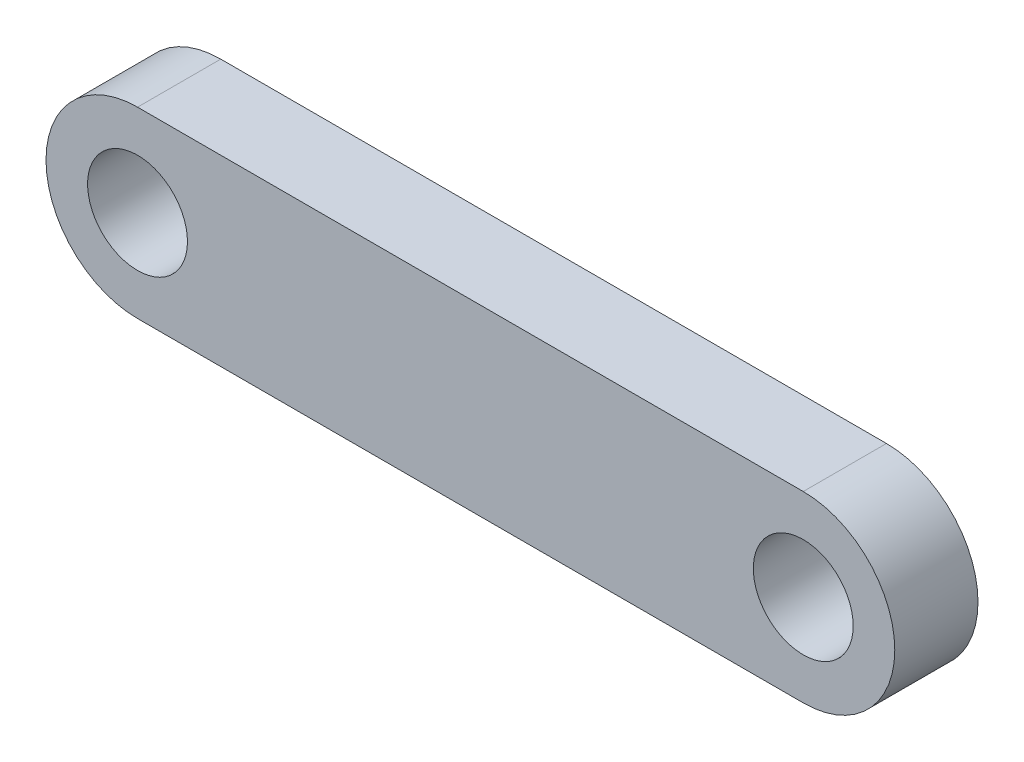
SolidWorks part; units mm, degrees
ref_plane "Front Plane" through (0, 0, 0) normal (0, 0, 1) x (1, 0, 0)
ref_plane "Top Plane" through (0, 0, 0) normal (0, 1, 0) x (1, 0, 0)
ref_plane "Right Plane" through (0, 0, 0) normal (1, 0, 0) x (0, 0, -1)
sketch "Sketch1" plane through (0, 0, 0) normal (0, 0, 1) x (1, 0, 0)
  line L0 (-20, 0) -> (20, 0) construction
  line L1 (-20, 5.5) -> (20, 5.5)
  line L2 (-20, -5.5) -> (20, -5.5)
  arc A0 (-20, 5.5) -> (-20, -5.5) centre (-20, 0) ccw
  arc A1 (20, -5.5) -> (20, 5.5) centre (20, 0) ccw
  circle A2 centre (-20, 0) radius 3
  circle A3 centre (20, 0) radius 3
  point P2 (0, 0)
  dimension "D3" = 6
  dimension "D1" = 11
  dimension "D2" = 40
extrude "Boss-Extrude1" add sketch "Sketch1" along normal mid plane 5
